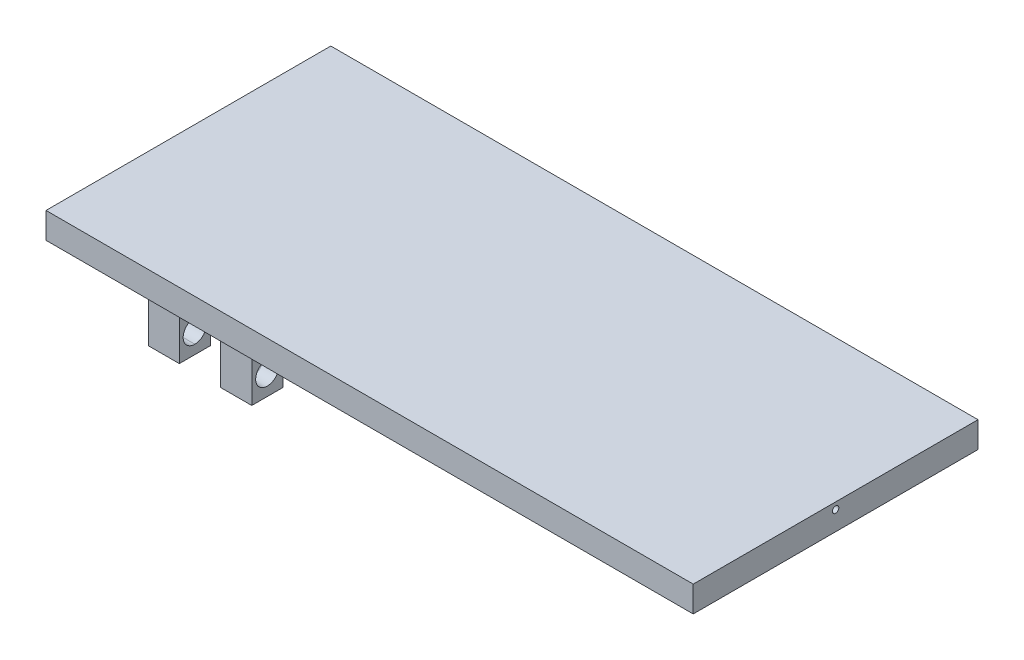
SolidWorks part; units mm, degrees
ref_plane "Front Plane" through (0, 0, 0) normal (0, 0, 1) x (1, 0, 0)
ref_plane "Top Plane" through (0, 0, 0) normal (0, 1, 0) x (1, 0, 0)
ref_plane "Right Plane" through (0, 0, 0) normal (1, 0, 0) x (0, 0, -1)
sketch "Sketch1" plane through (0, 0, 0) normal (0, 1, 0) x (1, 0, 0)
  line L0 (-14.339, 0) -> (110.661, 0)
  line L3 (8.161, 55) -> (110.661, 55)
  line L4 (110.661, 55) -> (110.661, 0)
  line L5 (8.161, 55) -> (-14.339, 55)
  line L6 (-14.339, 55) -> (-14.339, 0)
  dimension "D1" = 125
  dimension "D2" = 55
extrude "Boss-Extrude1" add sketch "Sketch1" along normal blind 5
sketch "Sketch3" plane through (0, 0, 0) normal (0, -1, 0) x (-1, 0, 0)
  line L0 (14.339, 55) -> (14.339, 0) construction
  line L1 (1.839, 47.75) -> (-4.161, 47.75)
  line L2 (1.839, 47.75) -> (1.839, 41.75)
  line L3 (1.839, 41.75) -> (-4.161, 41.75)
  line L4 (-4.161, 47.75) -> (-4.161, 41.75)
  line L5 (1.839, 13.25) -> (-4.161, 13.25)
  line L6 (1.839, 13.25) -> (1.839, 7.25)
  line L7 (1.839, 7.25) -> (-4.161, 7.25)
  line L8 (-4.161, 13.25) -> (-4.161, 7.25)
  line L9 (-12.161, 47.9346) -> (-18.161, 47.9346)
  line L10 (14.339, 0) -> (-110.661, 0) construction
  line L11 (-12.161, 47.9346) -> (-12.161, 41.9346)
  line L12 (-12.161, 41.9346) -> (-18.161, 41.9346)
  line L13 (-18.161, 47.9346) -> (-18.161, 41.9346)
  line L14 (-12.161, 13.2402) -> (-18.161, 13.2402)
  line L15 (-12.161, 13.2402) -> (-12.161, 7.2402)
  line L16 (-12.161, 7.2402) -> (-18.161, 7.2402)
  line L17 (-18.161, 13.2402) -> (-18.161, 7.2402)
  line L18 (-110.661, 0) -> (-110.661, 55) construction
  dimension "D1" = 34.5
  dimension "D2" = 6
  dimension "D3" = 6
  dimension "D4" = 6
  dimension "D5" = 6
  dimension "D6" = 12.5
  dimension "D7" = 6
  dimension "D8" = 7.25
  dimension "D9" = 6
  dimension "D10" = 8
  dimension "D11" = 6
  dimension "D12" = 6
  dimension "D13" = 8
  dimension "D14" = 92.5
extrude "Boss-Extrude2" add sketch "Sketch3" along normal blind 15
hole_wizard "#8 Clearance Hole2" positions "3DSketch2" profile "Sketch16" hole size "#8" standard "ANSI Inch"
sketch3d "3DSketch2"
  line L0 (-1.839, -15, -47.75) -> (-1.839, 0, -47.75) construction
  line L1 (-1.839, -15, -13.25) -> (-1.839, 0, -13.25) construction
  line L2 (-1.839, -15, -41.75) -> (-1.839, -15, -47.75) construction
  line L3 (-1.839, -15, -7.25) -> (-1.839, -15, -13.25) construction
  line L4 (18.161, -15, -47.9346) -> (18.161, -15, -41.9346) construction
  line L5 (18.161, -15, -47.9346) -> (18.161, 0, -47.9346) construction
  line L6 (18.161, -15, -7.2402) -> (18.161, 0, -7.2402) construction
  line L7 (18.161, -15, -13.2402) -> (18.161, -15, -7.2402) construction
  point P0 (-1.839, -11, -44.75)
  point P2 (-1.839, -11, -10.25)
  point P14 (18.161, -11, -44.9346)
  point P22 (18.161, -11, -10.2402)
  dimension "D1" = 3
  dimension "D2" = 3
  dimension "D3" = 4
  dimension "D4" = 4
  dimension "D5" = 4
  dimension "D6" = 3
  dimension "D7" = 3
  dimension "D8" = 4
sketch "Sketch16" plane through (-1.839, -11, -44.75) normal (0, 1, 0) x (0, 0, 1)
  line L0 (0, 0) -> (0, 18.3507)
  line L1 (0, 18.3507) -> (2.2479, 17)
  line L2 (2.2479, 17) -> (2.2479, 0)
  line L5 (2.2479, 0) -> (0, 0)
  line L10 (0, 18.3507) -> (-2.2479, 17) construction
  line L11 (0, -6.35) -> (0, 107.95) construction
  dimension "Hole Dia." = 4.4958
  dimension "Hole Depth" = 17
  dimension "Drill Angle" = 118
sketch "Sketch17" plane through (110.661, 0, 0) normal (1, 0, 0) x (0, 0, -1)
  line L0 (0, 5) -> (0, 0) construction
  circle A0 centre (27.5, 3.7125) radius 0.625
  dimension "D2" = 1.25
  dimension "D1" = 27.5
extrude "Cut-Extrude1" cut sketch "Sketch17" against normal blind 30
